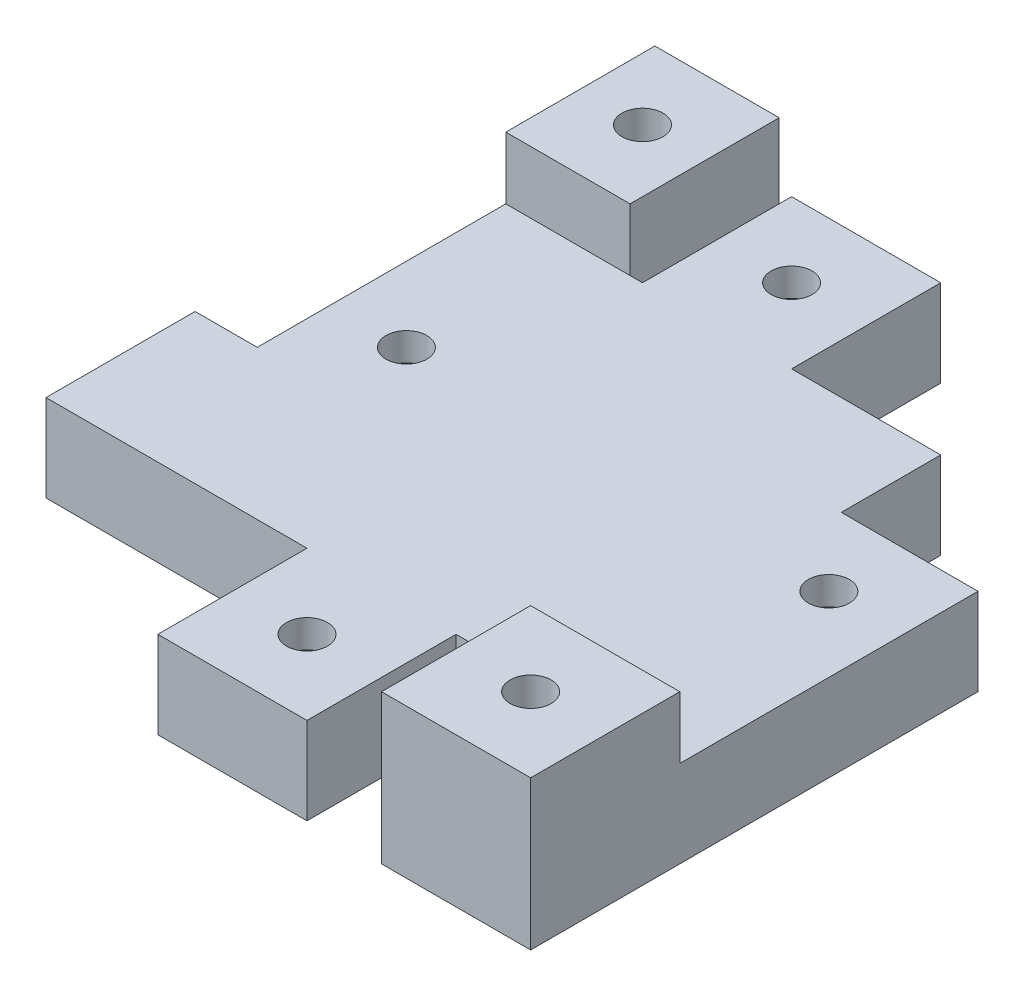
SolidWorks part; units mm, degrees
ref_plane "Front Plane" through (0, 0, 0) normal (0, 0, 1) x (1, 0, 0)
ref_plane "Top Plane" through (0, 0, 0) normal (0, 1, 0) x (1, 0, 0)
ref_plane "Right Plane" through (0, 0, 0) normal (1, 0, 0) x (0, 0, -1)
sketch "Sketch1" plane through (0, 0, 0) normal (0, 1, 0) x (1, 0, 0)
  line L1 (-5, 32) -> (7, 32)
  line L2 (-5, 32) -> (-5, 44)
  line L3 (-5, 44) -> (7, 44)
  line L4 (7, 32) -> (7, 44)
  line L5 (0, 0) -> (12, 0)
  line L6 (0, 0) -> (0, -12)
  line L7 (0, -12) -> (12, -12)
  line L8 (12, 0) -> (12, -12)
  line L9 (-16, 24) -> (-4, 24)
  line L10 (-16, 24) -> (-16, 12)
  line L11 (-16, 12) -> (-4, 12)
  line L12 (-4, 24) -> (-4, 12)
  line L13 (18, 24) -> (30, 24)
  line L14 (18, 24) -> (18, 12)
  line L15 (18, 12) -> (30, 12)
  line L16 (30, 24) -> (30, 12)
  circle A0 centre (6, -6) radius 1.65
  circle A1 centre (1, 38) radius 1.65
  circle A2 centre (-10, 18) radius 1.65
  circle A3 centre (24, 18) radius 1.65
  dimension "D5" = 3.3
  dimension "D6" = 6
  dimension "D7" = 6
  dimension "D8" = 6
  dimension "D9" = 6
  dimension "D10" = 44
  dimension "D11" = 5
  dimension "D16" = 6
  dimension "D17" = 6
  dimension "D20" = 12
  dimension "D22" = 6
  dimension "D23" = 6
  dimension "D25" = 18
  dimension "D12" = 10
  dimension "D15" = 18
  dimension "D1" = 12
  dimension "D2" = 12
  dimension "D3" = 12
  dimension "D4" = 12
  dimension "D13" = 12
  dimension "D14" = 12
  dimension "D18" = 0
  dimension "D19" = 0
  dimension "D21" = 12
  dimension "D24" = 18
extrude "Boss-Extrude1" add sketch "Sketch1" along normal blind 7
sketch "Sketch2" plane through (0, 7, 0) normal (0, 1, 0) x (1, 0, 0)
  line L1 (9.2332, -6) -> (7.6166, -3.2)
  line L2 (7.6166, -3.2) -> (4.3834, -3.2)
  line L3 (4.3834, -3.2) -> (2.7668, -6)
  line L4 (2.7668, -6) -> (4.3834, -8.8)
  line L5 (4.3834, -8.8) -> (7.6166, -8.8)
  line L6 (7.6166, -8.8) -> (9.2332, -6)
  line L7 (20.7668, 18) -> (22.3834, 15.2)
  line L8 (22.3834, 15.2) -> (25.6166, 15.2)
  line L9 (25.6166, 15.2) -> (27.2332, 18)
  line L10 (27.2332, 18) -> (25.6166, 20.8)
  line L11 (25.6166, 20.8) -> (22.3834, 20.8)
  line L12 (22.3834, 20.8) -> (20.7668, 18)
  line L13 (-2.2332, 38) -> (-0.6166, 35.2)
  line L14 (-0.6166, 35.2) -> (2.6166, 35.2)
  line L15 (2.6166, 35.2) -> (4.2332, 38)
  line L16 (4.2332, 38) -> (2.6166, 40.8)
  line L17 (2.6166, 40.8) -> (-0.6166, 40.8)
  line L18 (-0.6166, 40.8) -> (-2.2332, 38)
  line L19 (-13.2332, 18) -> (-11.6166, 15.2)
  line L20 (-11.6166, 15.2) -> (-8.3834, 15.2)
  line L21 (-8.3834, 15.2) -> (-6.7668, 18)
  line L22 (-6.7668, 18) -> (-8.3834, 20.8)
  line L23 (-8.3834, 20.8) -> (-11.6166, 20.8)
  line L24 (-11.6166, 20.8) -> (-13.2332, 18)
  circle A0 centre (6, -6) radius 2.8 construction
  circle A1 centre (24, 18) radius 2.8 construction
  circle A2 centre (1, 38) radius 2.8 construction
  circle A3 centre (-10, 18) radius 2.8 construction
  dimension "D1" = 5.6
extrude "Cut-Extrude1" cut sketch "Sketch2" against normal blind 2.5 from offset 2.25 offset against normal yes
sketch "Sketch3" plane through (0, 7, 0) normal (0, 1, 0) x (1, 0, 0)
  line L1 (-21, 0) -> (30, 0)
  line L2 (-21, 0) -> (-21, 12)
  line L3 (-21, 12) -> (30, 12)
  line L4 (30, 0) -> (30, 12)
  line L5 (18, 12) -> (-4, 12)
  line L6 (18, 12) -> (18, 24)
  line L7 (18, 24) -> (-4, 24)
  line L8 (-4, 12) -> (-4, 24)
  line L9 (-16, 24) -> (19, 24)
  line L10 (-16, 24) -> (-16, 32)
  line L11 (-16, 32) -> (19, 32)
  line L12 (19, 24) -> (19, 32)
  line M4 (12, 0) -> (0, 0)
extrude "Boss-Extrude2" add sketch "Sketch3" against normal blind 7 contours L9 L12 L11 L10 L7 | L8 L3 L6 L7 | L1 L4 L3 L2 M4
sketch "Sketch4" plane through (0, 7, 0) normal (0, 1, 0) x (1, 0, 0)
  line L1 (-16, 32) -> (-6, 32)
  line L2 (-16, 32) -> (-16, 44)
  line L3 (-16, 44) -> (-6, 44)
  line L4 (-6, 32) -> (-6, 44)
  line L6 (30, 0) -> (18, 0)
  line L7 (30, 0) -> (30, -12)
  line L8 (30, -12) -> (18, -12)
  line L9 (18, 0) -> (18, -12)
  circle A0 centre (-11, 38) radius 1.65
  circle A1 centre (24, -6) radius 1.65
  dimension "D5" = 3.3
  dimension "D6" = 6
  dimension "D7" = 6
  dimension "D8" = 6
  dimension "D9" = 5
  dimension "D1" = 12
  dimension "D2" = 10
  dimension "D3" = 12
  dimension "D4" = 12
extrude "Boss-Extrude3" add sketch "Sketch4" against normal blind 7
sketch "Sketch5" plane through (0, 7, 0) normal (0, 1, 0) x (1, 0, 0)
  line L1 (-7.7668, 38) -> (-9.3834, 40.8)
  line L2 (-9.3834, 40.8) -> (-12.6166, 40.8)
  line L3 (-12.6166, 40.8) -> (-14.2332, 38)
  line L4 (-14.2332, 38) -> (-12.6166, 35.2)
  line L5 (-12.6166, 35.2) -> (-9.3834, 35.2)
  line L6 (-9.3834, 35.2) -> (-7.7668, 38)
  line L7 (27.2332, -6) -> (25.6166, -3.2)
  line L8 (25.6166, -3.2) -> (22.3834, -3.2)
  line L9 (22.3834, -3.2) -> (20.7668, -6)
  line L10 (20.7668, -6) -> (22.3834, -8.8)
  line L11 (22.3834, -8.8) -> (25.6166, -8.8)
  line L12 (25.6166, -8.8) -> (27.2332, -6)
  circle A0 centre (-11, 38) radius 2.8 construction
  circle A1 centre (24, -6) radius 2.8 construction
  dimension "D1" = 5.6
  dimension "D2" = 5.6
extrude "Cut-Extrude2" cut sketch "Sketch5" against normal blind 2.5 from offset 2.25 offset against normal yes
sketch "Sketch6" plane through (0, 7, 0) normal (0, 1, 0) x (1, 0, 0)
  line L1 (-6, 32) -> (-16, 32)
  line L2 (-6, 32) -> (-6, 44)
  line L3 (-6, 44) -> (-16, 44)
  line L4 (-16, 32) -> (-16, 44)
  line L5 (30, -12) -> (18, -12)
  line L6 (30, -12) -> (30, 0)
  line L7 (30, 0) -> (18, 0)
  line L8 (18, -12) -> (18, 0)
  circle A0 centre (-11, 38) radius 1.65
  circle A1 centre (24, -6) radius 1.65
extrude "Boss-Extrude4" add sketch "Sketch6" along normal blind 5
